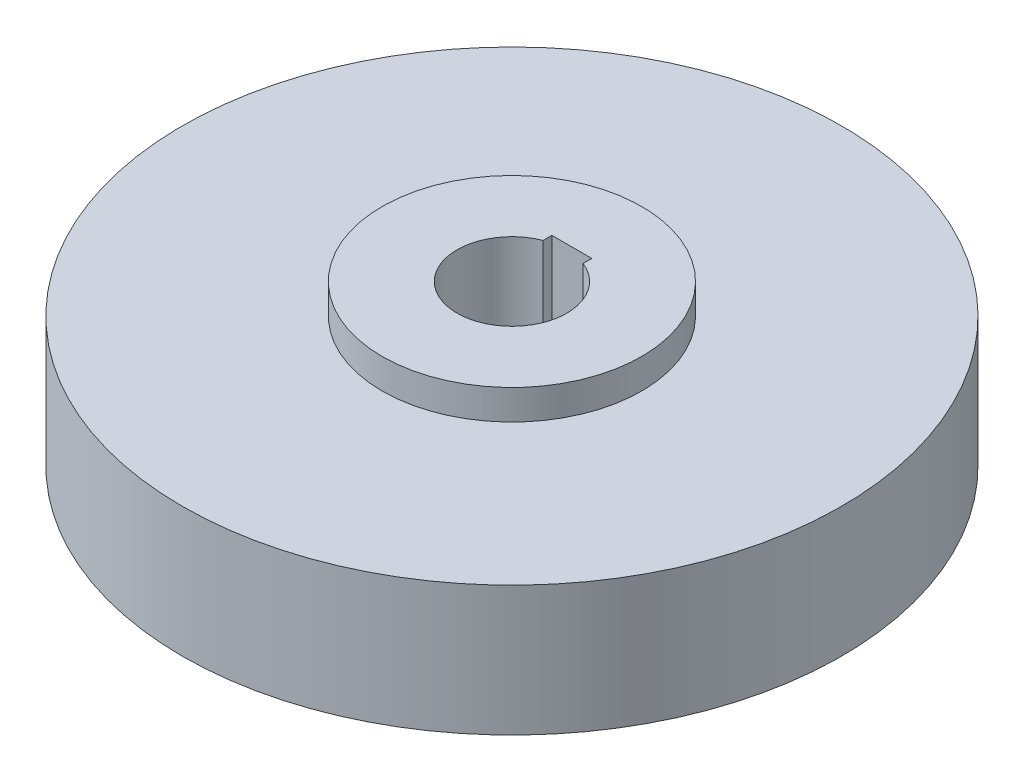
SolidWorks part; units mm, degrees
ref_plane "Front Plane" through (0, 0, 0) normal (0, 0, 1) x (1, 0, 0)
ref_plane "Top Plane" through (0, 0, 0) normal (0, 1, 0) x (1, 0, 0)
ref_plane "Right Plane" through (0, 0, 0) normal (1, 0, 0) x (0, 0, -1)
sketch "Sketch1" plane through (0, 0, 0) normal (0, 1, 0) x (1, 0, 0)
  circle A0 centre (0, 0) radius 33
  dimension "D1" = 66
extrude "Boss-Extrude1" add sketch "Sketch1" along normal blind 13
sketch "Sketch2" plane through (0, 13, 0) normal (0, 1, 0) x (1, 0, 0)
  circle A0 centre (0, 0) radius 13
  dimension "D1" = 26
extrude "Boss-Extrude2" add sketch "Sketch2" along normal blind 3
sketch "Sketch3" plane through (0, 16, 0) normal (0, 1, 0) x (1, 0, 0)
  line L1 (-2, 6) -> (2, 6)
  line L2 (-2, 6) -> (-2, 5)
  line L3 (-2, 5) -> (2, 5)
  line L4 (2, 6) -> (2, 5)
  line L5 (0, 5) -> (0, 6) construction
  line L6 (-2, 5.5) -> (2, 5.5) construction
  circle A0 centre (0, 0) radius 5.5
  point P3 (0, 5.5)
  dimension "D1" = 11
  dimension "D2" = 6
  dimension "D3" = 4
extrude "Cut-Extrude1" cut sketch "Sketch3" against normal through all both and the other way through all contours L2 A0 L4 L3 | A0 L4 L1 L2 | L4 A0 L2 L3
